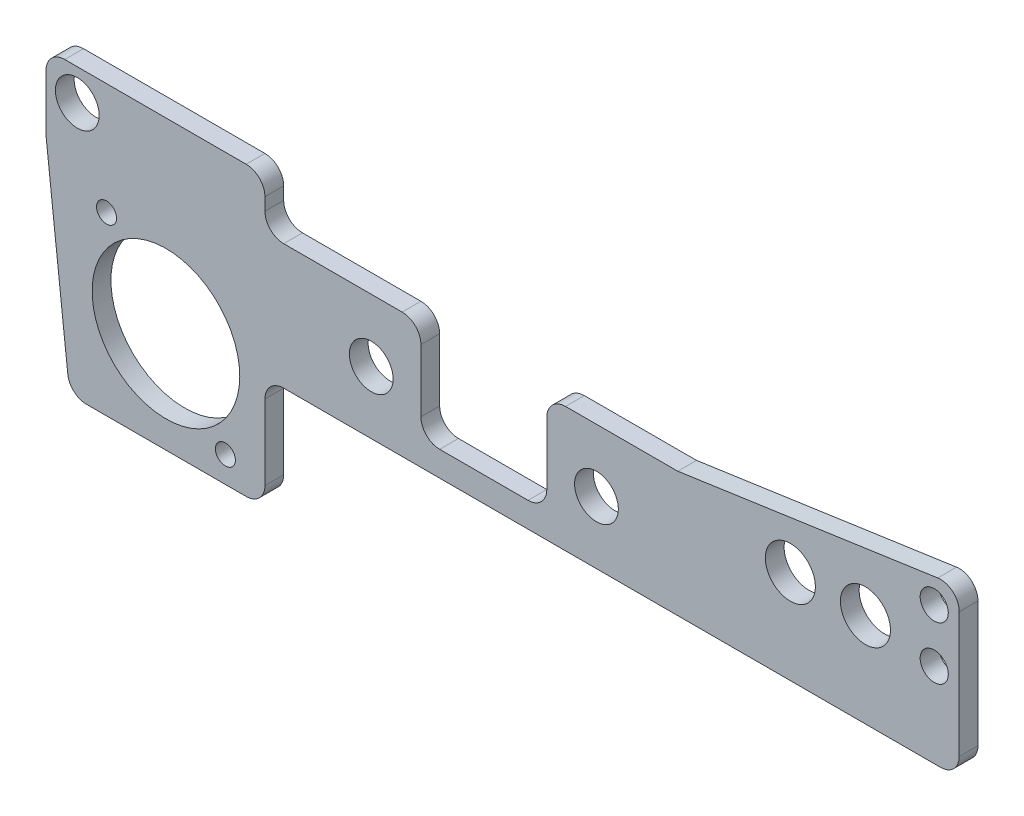
SolidWorks part; units mm, degrees
ref_plane "Plan de face" through (0, 0, 0) normal (0, 0, 1) x (1, 0, 0)
ref_plane "Plan de dessus" through (0, 0, 0) normal (0, 1, 0) x (1, 0, 0)
ref_plane "Plan de droite" through (0, 0, 0) normal (1, 0, 0) x (0, 0, -1)
sketch "Esquisse1" plane through (0, 0, 0) normal (0, 0, 1) x (1, 0, 0)
  line L1 (0, 0) -> (146, 0)
  line L2 (0, 0) -> (0, 20)
  line L3 (0, 20) -> (146, 20)
  line L4 (146, 0) -> (146, 20)
  dimension "D1" = 146
  dimension "D2" = 20
extrude "Boss.-Extru.1" add sketch "Esquisse1" along normal blind 3
sketch "Esquisse2" plane through (0, 0, 3) normal (0, 0, 1) x (1, 0, 0)
  line L0 (88, 10) -> (52, 10) construction
  line L1 (146, 20) -> (0, 20) construction
  line L2 (146, 0) -> (146, 20) construction
  circle A0 centre (52, 10) radius 3.5
  circle A1 centre (88, 10) radius 3.5
  dimension "D1" = 7
  dimension "D2" = 36
  dimension "D3" = 10
  dimension "D4" = 58
extrude "Enlèv. mat.-Extru.3" cut sketch "Esquisse2" against normal through all
sketch "Esquisse6" plane through (0, 20, 0) normal (0, 1, 0) x (1, 0, 0)
  line L0 (146, 0) -> (0, 0) construction
  line L1 (0, -3) -> (35, -3)
  line L2 (0, -3) -> (0, 0)
  line L3 (0, 0) -> (35, 0)
  line L4 (35, -3) -> (35, 0)
  dimension "D1" = 35
extrude "Boss.-Extru.3" add sketch "Esquisse6" along normal blind 8
sketch "Esquisse8" plane through (0, 0, 3) normal (0, 0, 1) x (1, 0, 0)
  line L0 (52, 10) -> (52, 20) construction
  line L1 (146, 20) -> (35, 20) construction
  circle A0 centre (5, 23) radius 3.5
  point P2 (52.7203, 20)
  dimension "D1" = 7
  dimension "D2" = 47
  dimension "D3" = 13
extrude "Enlèv. mat.-Extru.4" cut sketch "Esquisse8" against normal blind 8 contours A0
sketch "Esquisse9" plane through (0, 0, 3) normal (0, 0, 1) x (1, 0, 0)
  line L0 (35, 28) -> (35, -5.6056) construction
sketch "Esquisse7" plane through (0, 0, 0) normal (0, -1, 0) x (1, 0, 0)
  line L0 (0, 0) -> (146, 0) construction
  line L1 (0, 3) -> (35, 3)
  line L2 (0, 3) -> (0, 0)
  line L3 (0, 0) -> (35, 0)
  line L4 (35, 3) -> (35, 0)
extrude "Boss.-Extru.4" add sketch "Esquisse7" along normal blind 24 contours L1 L4 L3 L2
fillet "Congé2" radius 3 8 edges at (35, 0, 1.5) (35, 20, 1.5) (35, 28, 1.5) (0, 28, 1.5) (35, -24, 1.5) (0, -24, 1.5) (146, 0, 1.5) (146, 20, 1.5)
sketch "Esquisse10" plane through (0, 0, 3) normal (0, 0, 1) x (1, 0, 0)
  line L0 (143, 20) -> (38, 20) construction
  line L1 (80.0636, 20) -> (59.9364, 20)
  line L2 (80.0636, 20) -> (80.0636, 4)
  line L3 (80.0636, 4) -> (59.9364, 4)
  line L4 (59.9364, 20) -> (59.9364, 4)
  line L5 (88, 10) -> (80.0636, 10) construction
  line L6 (59.9364, 10) -> (52, 10) construction
  line L7 (88, 6.5) -> (51.0199, 6.64) construction
  line L8 (38, 0) -> (143, 0) construction
  circle A2 centre (88, 10) radius 3.5 construction
  circle A3 centre (52, 10) radius 3.5 construction
  dimension "D1" = 4
extrude "Enlèv. mat.-Extru.5" cut sketch "Esquisse10" against normal blind 24
fillet "Congé3" radius 3 4 edges at (59.9364, 20, 1.5) (59.9364, 4, 1.5) (80.0636, 4, 1.5) (80.0636, 20, 1.5)
sketch "Esquisse14" plane through (0, 0, 3) normal (0, 0, 1) x (1, 0, 0)
  line L0 (146, 10) -> (146, 26.5)
  line L1 (146, 3) -> (146, 17) construction
  line L2 (146, 26.5) -> (101, 20)
  line L3 (143, 20) -> (83.0636, 20) construction
  line L4 (101, 20) -> (146, 10)
  dimension "D1" = 45
  dimension "D2" = 16.5
extrude "Boss.-Extru.5" add sketch "Esquisse14" against normal blind 3
sketch "Esquisse13" plane through (0, 0, 3) normal (0, 0, 1) x (1, 0, 0)
  line L0 (142, -6.1037) -> (142, 39.2519) construction
  line L1 (88, 10) -> (88, 6.5) construction
  line L2 (82.1519, 13.5) -> (157.1519, 13.5) construction
  line L3 (38, 0) -> (143, 0) construction
  circle A0 centre (88, 10) radius 3.5 construction
  circle A1 centre (142, 22) radius 2.25
  circle A2 centre (142, 13.5) radius 2.25
  point P11 (142, 11.4931)
  point P12 (0, 0)
  dimension "D3" = 4.5
  dimension "D4" = 4.5
  dimension "D1" = 54
  dimension "D2" = 8.5
  dimension "D5" = 13.5
extrude "Enlèv. mat.-Extru.6" cut sketch "Esquisse13" against normal blind 24
fillet "Congé4" radius 3 1 edges at (146, 26.5, 1.5)
sketch "Esquisse16" plane through (0, 0, 3) normal (0, 0, 1) x (1, 0, 0)
  line L0 (19.1759, -1.8702) -> (19.1759, -20.5272) construction
  line L1 (19.1759, -1.8702) -> (19.1759, 14.0117) construction
  line L2 (28.6787, -13.8385) -> (19.1759, -13.6702) construction
  line L4 (19.1759, 9.9298) -> (9.6787, 10.1615) construction
  circle A0 centre (19.1759, -1.8702) radius 11.8
  circle A1 centre (9.6787, 10.1615) radius 1.6
  circle A2 centre (28.6787, -13.8385) radius 1.6
  dimension "D1" = 24
  dimension "D2" = 19
  dimension "D3" = 9.5
extrude "Enlèv. mat.-Extru.7" cut sketch "Esquisse16" against normal blind 3
sketch "Esquisse17" plane through (0, 0, 3) normal (0, 0, 1) x (1, 0, 0)
  line L0 (35, -18) -> (3.7823, -18)
  line L1 (35, -21) -> (35, -3) construction
  line L2 (3.7823, -18) -> (0, 15.9811)
  line L3 (3, 28) -> (32, 28) construction
  line L4 (0, 25) -> (0, -21) construction
  line L5 (0, 15.9811) -> (0, -26.9415)
  line L6 (0, -26.9415) -> (35, -26.9415)
  line L7 (35, -26.9415) -> (35, -18)
  point P4 (19.3912, -18)
  dimension "D1" = 46
extrude "Enlèv. mat.-Extru.11" cut sketch "Esquisse17" against normal blind 3
fillet "Congé10" radius 3 3 edges at (35, -18, 1.5) (3.7823, -18, 1.5) (0, 15.9811, 1.5)
sketch "Esquisse18" plane through (0, 0, 3) normal (0, 0, 1) x (1, 0, 0)
  line L0 (134.4219, 15) -> (103.2167, 15) construction
  line L1 (38, 0) -> (143, 0) construction
  line L2 (146, 3) -> (146, 23.0355) construction
  circle A0 centre (131, 15) radius 4
  circle A1 centre (119, 15) radius 4
  point P8 (0, 0)
  point P9 (0, 0)
  point P10 (0, 0)
  dimension "D2" = 8
  dimension "D3" = 8
  dimension "D1" = 15
  dimension "D4" = 12
  dimension "D5" = 15
extrude "Enlèv. mat.-Extru.12" cut sketch "Esquisse18" against normal blind 3
